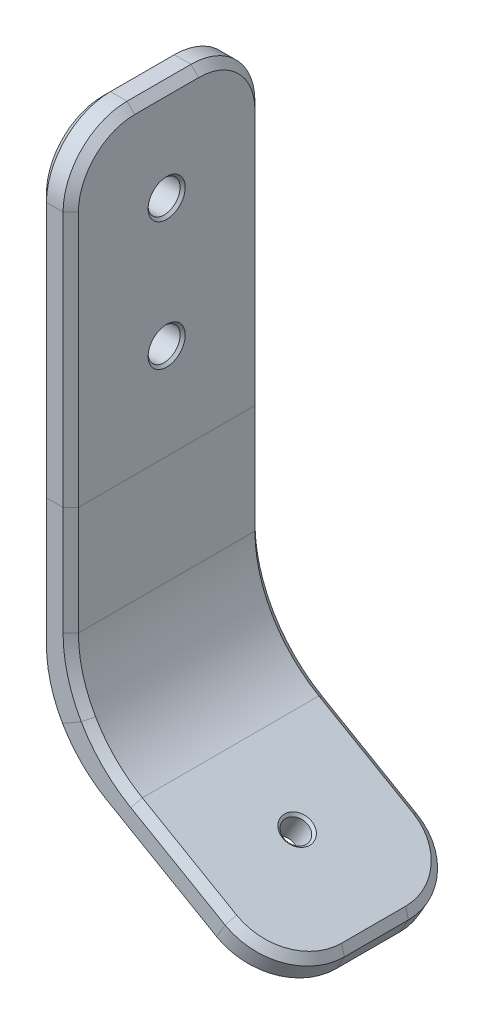
SolidWorks part; units mm, degrees
ref_plane "Front Plane" through (0, 0, 0) normal (0, 0, 1) x (1, 0, 0)
ref_plane "Top Plane" through (0, 0, 0) normal (0, 1, 0) x (1, 0, 0)
ref_plane "Right Plane" through (0, 0, 0) normal (1, 0, 0) x (0, 0, -1)
sketch "Sketch1" plane through (0, 0, 0) normal (0, 0, 1) x (1, 0, 0)
  line L0 (0, 0) -> (0, -31.75)
  line L1 (0, -31.75) -> (0, -50.8)
  line L2 (0, -50.8) -> (21.997, -63.5)
  dimension "D2" = 19.05
  dimension "D1" = 31.75
  dimension "D3" = 180
  dimension "D4" = 120
  dimension "D5" = 25.4
sketch "Sketch2" plane through (0, 0, 0) normal (0, 1, 0) x (1, 0, 0)
  line L1 (-1.5875, -9.525) -> (1.5875, -9.525)
  line L2 (-1.5875, -9.525) -> (-1.5875, 9.525)
  line L3 (-1.5875, 9.525) -> (1.5875, 9.525)
  line L4 (1.5875, -9.525) -> (1.5875, 9.525)
  line L5 (-1.5875, -9.525) -> (1.5875, 9.525) construction
  line L6 (-1.5875, 9.525) -> (1.5875, -9.525) construction
  point P0 (0, 0)
  dimension "D1" = 3.175
  dimension "D2" = 19.05
sweep "Sweep1" add profiles "Sketch2" path "Sketch1"
hole_wizard "1/8 (0.125) Diameter Hole1" positions "Sketch3" profile "Sketch4" hole size "1/8" standard "ANSI Inch" end condition through all
sketch "Sketch3" plane through (1.5875, 0, 0) normal (1, 0, 0) x (0, 0, -1)
  line L0 (0, -22.225) -> (0, -31.75) construction
  line L1 (9.525, -31.75) -> (-9.525, -31.75) construction
  line L3 (0, -9.525) -> (0, 0) construction
  point P0 (0, -9.525)
  point P2 (0, -22.225)
  dimension "D1" = 12.7
sketch "Sketch4" plane through (1.5875, -9.525, 0) normal (0, 1, 0) x (0, 0, -1)
  line L0 (0, 0) -> (0, 3.175)
  line L1 (0, 3.175) -> (1.5875, 3.175)
  line L2 (1.5875, 3.175) -> (1.5875, 0)
  line L5 (1.5875, 0) -> (0, 0)
  line L11 (0, -6.35) -> (0, 107.95) construction
  dimension "Thru Hole Dia." = 3.175
  dimension "Thru Hole Depth" = 3.175
hole_wizard "3/32 (0.09375) Diameter Hole2" positions "Sketch5" profile "Sketch6" hole size "3/32" standard "ANSI Inch" end condition through all
sketch "Sketch5" plane through (-21.2033, -36.7252, 0) normal (0.5, 0.866, 0) x (0.866, -0.5, 0)
  line L1 (50.8, -9.525) -> (50.8, 9.525) construction
  point P0 (41.275, 0)
  dimension "D1" = 9.525
sketch "Sketch6" plane through (14.5419, -57.3627, 0) normal (0, 0, 1) x (-0.866, 0.5, 0)
  line L0 (0, 0) -> (0, 14.5704)
  line L1 (0, 14.5704) -> (1.1906, 14.5704)
  line L2 (1.1906, 14.5704) -> (1.1906, 0)
  line L5 (1.1906, 0) -> (0, 0)
  line L11 (0, -6.35) -> (0, 107.95) construction
  dimension "Thru Hole Dia." = 2.3812
  dimension "Thru Hole Depth" = 14.5704
fillet "Fillet1" radius 12.7 2 edges at (-1.5875, -51.7165, 0) (1.5875, -49.8835, 0)
fillet "Fillet2" radius 6.35 4 edges at (21.997, -63.5, -9.525) (21.997, -63.5, 9.525) (0, 0, -9.525) (0, 0, 9.525)
chamfer "Chamfer3" distance 0.762 angle 45 32 edges at (-1.5875, -38.0671, -9.525) (-1.1548, -47.6712, -9.525) (2.1322, -53.3645, -9.525) (-1.5875, -19.05, -9.525) (10.2333, -58.5413, -9.525) (-1.5875, -1.8599, -7.6651) (19.5926, -63.9449, -7.6651) (-1.5875, 0, 0) (21.2033, -64.8748, 0) (-1.5875, -1.8599, 7.6651) (19.5926, -63.9449, 7.6651) (-1.5875, -19.05, 9.525) (10.2333, -58.5413, 9.525) (2.1322, -53.3645, 9.525) (-1.1548, -47.6712, 9.525) (-1.5875, -38.0671, 9.525) (1.5875, -37.1506, -9.525) (2.0202, -45.8381, -9.525) (5.3072, -51.5314, -9.525) (1.5875, -19.05, -9.525) (12.6145, -56.2499, -9.525) (1.5875, -1.8599, -7.6651) (21.1801, -61.1952, -7.6651) (1.5875, 0, 0) (22.7908, -62.1252, 0) (1.5875, -1.8599, 7.6651) (21.1801, -61.1952, 7.6651) (1.5875, -19.05, 9.525) (12.6145, -56.2499, 9.525) (5.3072, -51.5314, 9.525) (2.0202, -45.8381, 9.525) (1.5875, -37.1506, 9.525)
chamfer "Chamfer2" distance 0.254 angle 45 6 edges at (1.5875, -22.225, -1.5875) (-1.5875, -22.225, -1.5875) (1.5875, -9.525, -1.5875) (-1.5875, -9.525, -1.5875) (13.5108, -56.7674, 0) (11.9233, -59.517, 0)
